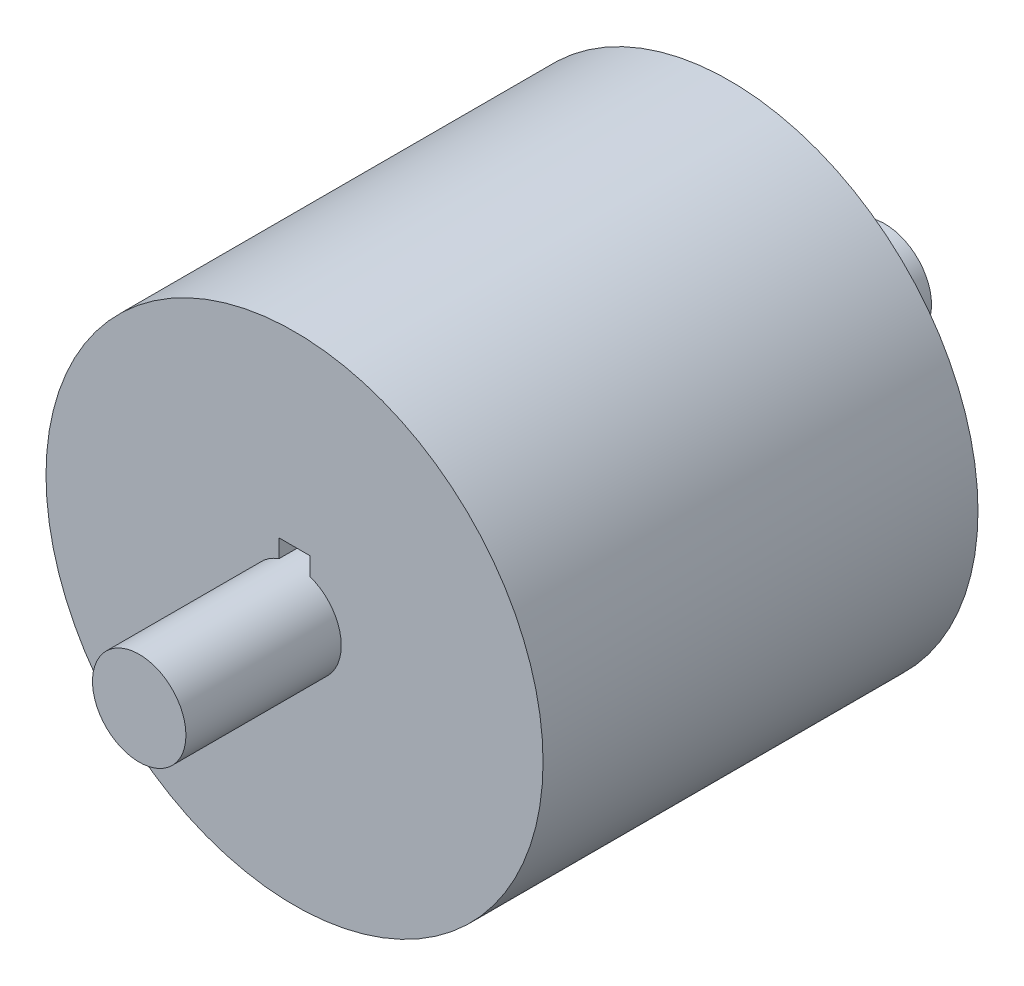
SolidWorks part; units mm, degrees
material "6061 Alloy"
ref_plane "Front Plane" through (0, 0, 0) normal (0, 0, 1) x (1, 0, 0)
ref_plane "Top Plane" through (0, 0, 0) normal (0, 1, 0) x (1, 0, 0)
ref_plane "Right Plane" through (0, 0, 0) normal (1, 0, 0) x (0, 0, -1)
sketch "Sketch1" plane through (0, 0, 0) normal (0, 0, 1) x (1, 0, 0)
  circle A0 centre (0, 0) radius 12.7
  dimension "D1" = 25.4
extrude "Extrude1" add sketch "Sketch1" along normal mid plane 22.225
sketch "Sketch2" plane through (0, 0, 11.1125) normal (0, 0, 1) x (1, 0, 0)
  line L1 (-0.7938, 3.175) -> (0.7937, 3.175)
  line L2 (-0.7938, 3.175) -> (-0.7937, 1.5875)
  line L3 (-0.7937, 1.5875) -> (0.7938, 1.5875)
  line L4 (0.7937, 3.175) -> (0.7938, 1.5875)
  line L5 (-0.7938, 3.175) -> (0.7938, 1.5875) construction
  line L6 (-0.7937, 1.5875) -> (0.7937, 3.175) construction
  circle A0 centre (0, 0) radius 2.3813
  point P3 (0, 2.3813)
  dimension "D1" = 4.7625
  dimension "D2" = 1.5875
extrude "Extrude2" cut sketch "Sketch2" against normal through all contours L2 A0 L4 L3 | A0 L4 L1 L2 | L4 A0 L2 L3
sketch "Sketch4" plane through (0, 0, 0) normal (0, 0, 1) x (1, 0, 0)
  circle A0 centre (0, 0) radius 2.3876
  dimension "D1" = 4.7752
extrude "Boss-Extrude1" add sketch "Sketch4" along normal mid plane 38.1
